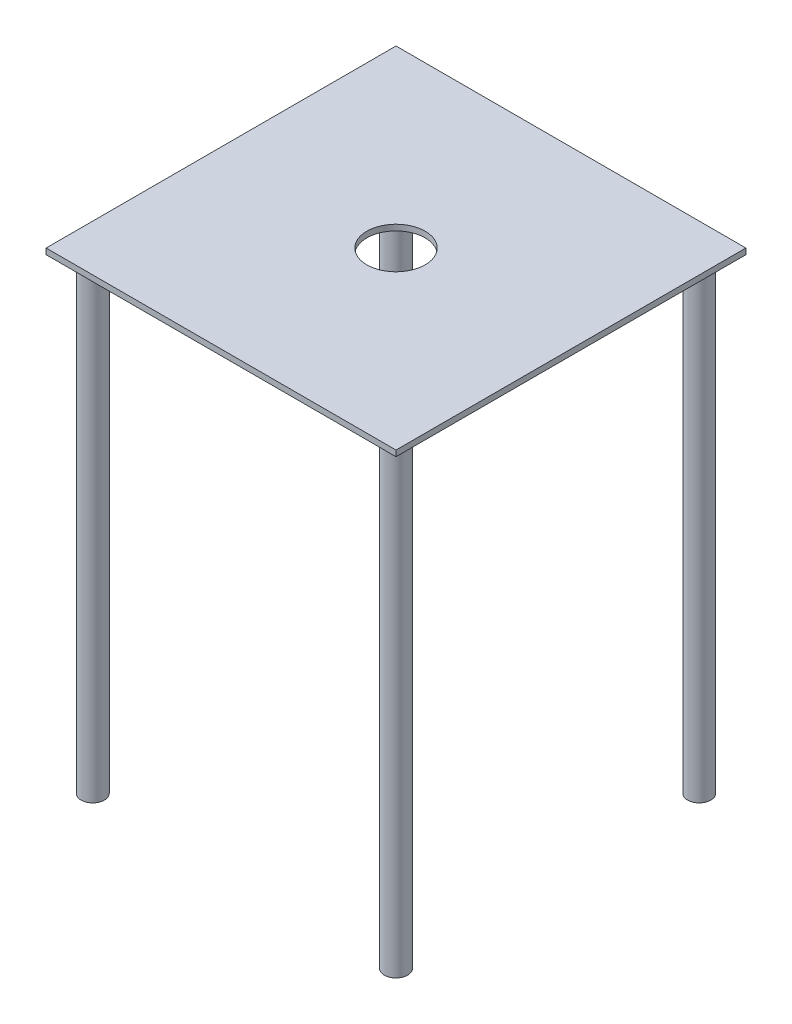
SolidWorks part; units mm, degrees
ref_plane "Front Plane" through (0, 0, 0) normal (0, 0, 1) x (1, 0, 0)
ref_plane "Top Plane" through (0, 0, 0) normal (0, 1, 0) x (1, 0, 0)
ref_plane "Right Plane" through (0, 0, 0) normal (1, 0, 0) x (0, 0, -1)
sketch "Sketch1" plane through (0, 0, 0) normal (0, 1, 0) x (1, 0, 0)
  line L0 (0, -190.5) -> (0, 0) construction
  line L1 (-190.5, 190.5) -> (190.5, 190.5)
  line L2 (-190.5, 190.5) -> (-190.5, -190.5)
  line L3 (-190.5, -190.5) -> (190.5, -190.5)
  line L4 (190.5, 190.5) -> (190.5, -190.5)
  line L5 (0, 0) -> (190.5, 0) construction
  dimension "D1" = 381
  dimension "D2" = 381
extrude "Extrude1" add sketch "Sketch1" along normal blind 6.35
sketch "Sketch2" plane through (0, 6.35, 0) normal (0, 1, 0) x (-1, 0, 0)
  circle A0 centre (0, 0) radius 31.75
  dimension "D1" = 63.5
extrude "Extrude2" cut sketch "Sketch2" against normal through all
sketch "Sketch3" plane through (0, 0, 0) normal (0, 1, 0) x (1, 0, 0)
  line L0 (0, 0) -> (0, 190.5) construction
  line L1 (190.5, 190.5) -> (-190.5, 190.5) construction
  line L2 (0, 0) -> (190.5, 0) construction
  line L3 (190.5, -190.5) -> (190.5, 190.5) construction
  circle A0 centre (165.1, 165.1) radius 12.7
  circle A1 centre (-165.1, 165.1) radius 12.7
  circle A2 centre (165.1, -165.1) radius 12.7
  circle A3 centre (-165.1, -165.1) radius 12.7
  dimension "D1" = 25.4
  dimension "D2" = 25.4
  dimension "D3" = 25.4
extrude "Extrude3" add sketch "Sketch3" against normal blind 508 separate body
